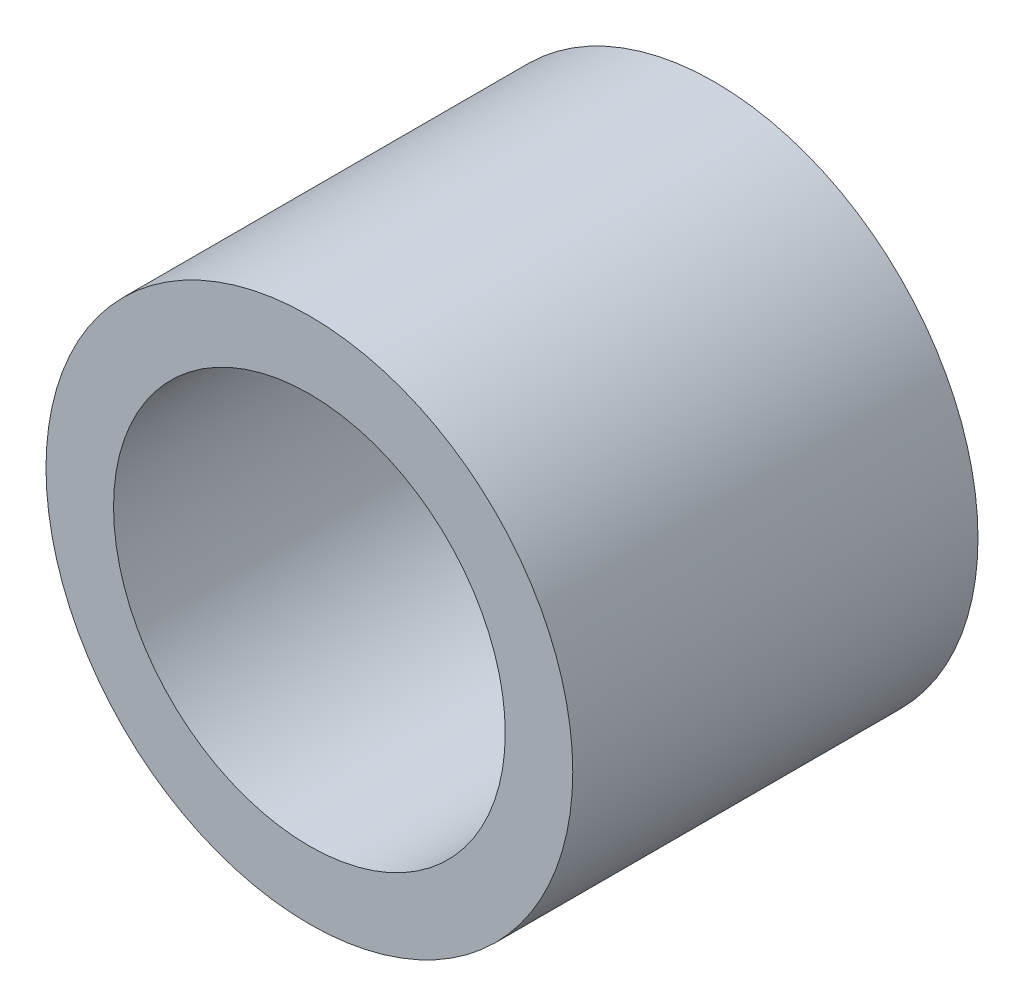
SolidWorks part; units mm, degrees
ref_plane "Front Plane" through (0, 0, 0) normal (0, 0, 1) x (1, 0, 0)
ref_plane "Top Plane" through (0, 0, 0) normal (0, 1, 0) x (1, 0, 0)
ref_plane "Right Plane" through (0, 0, 0) normal (1, 0, 0) x (0, 0, -1)
sketch "Sketch1" plane through (0, 0, 0) normal (0, 0, 1) x (1, 0, 0)
  circle A0 centre (0, 0) radius 3.9
  circle A1 centre (0, 0) radius 2.9
  dimension "D1" = 7.8
  dimension "D2" = 1
extrude "Boss-Extrude1" add sketch "Sketch1" along normal blind 6
